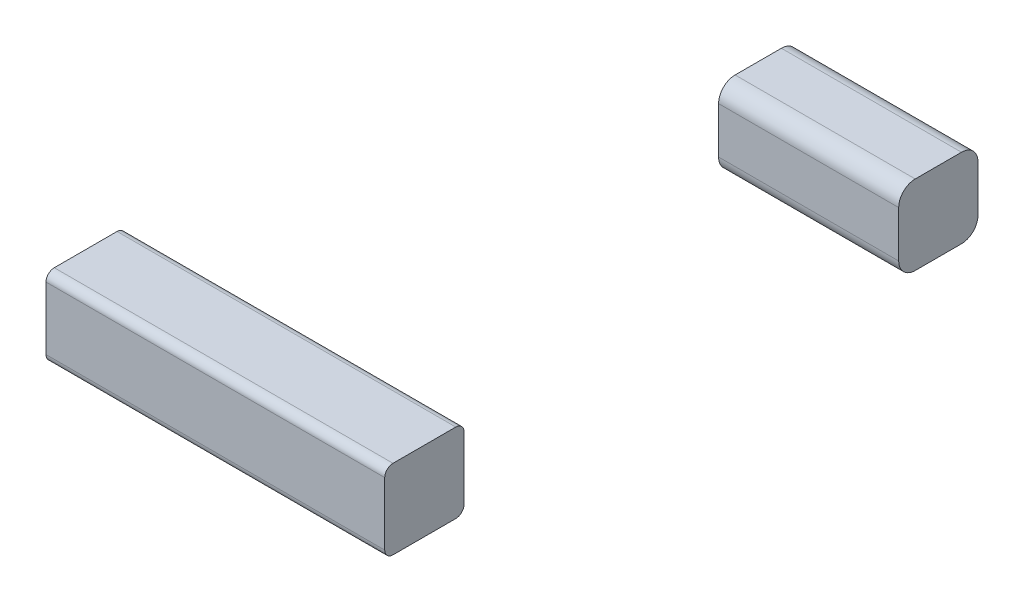
SolidWorks part; units mm, degrees
ref_plane "前视基准面" through (0, 0, 0) normal (0, 0, 1) x (1, 0, 0)
ref_plane "上视基准面" through (0, 0, 0) normal (0, 1, 0) x (1, 0, 0)
ref_plane "右视基准面" through (0, 0, 0) normal (1, 0, 0) x (0, 0, -1)
sketch "草图1" plane through (0, 0, 0) normal (0, 1, 0) x (1, 0, 0)
  line L1 (-12.2772, 15.4322) -> (-7.2772, 15.4322)
  line L2 (-12.2772, 15.4322) -> (-12.2772, 20.4322)
  line L3 (-12.2772, 20.4322) -> (-7.2772, 20.4322)
  line L4 (-7.2772, 15.4322) -> (-7.2772, 20.4322)
  line L5 (-12.2772, 15.4322) -> (-7.2772, 20.4322) construction
  line L6 (-12.2772, 20.4322) -> (-7.2772, 15.4322) construction
  circle A0 centre (-9.7772, 17.9322) radius 4.9
  dimension "D1" = 9.8
  dimension "D2" = 5
  dimension "D3" = 5
extrude "凸台-拉伸1" add sketch "草图1" along normal blind 5
sketch "草图2" plane through (0, 0, 0) normal (0, 1, 0) x (1, 0, 0)
  line L0 (-20.4935, 24.5269) -> (-10.4935, 24.5269)
  line L1 (-10.4935, 24.5269) -> (-10.4935, 29.5269)
  line L2 (-10.4935, 29.5269) -> (-20.4935, 29.5269)
  line L3 (-20.4935, 29.5269) -> (-20.4935, 24.5269)
  dimension "D1" = 10
  dimension "D2" = 5
extrude "凸台-拉伸2" add sketch "草图2" along normal blind 5 separate body
sketch "草图3" plane through (0, 5, 0) normal (0, 1, 0) x (1, 0, 0)
  circle A0 centre (-9.7772, 17.9322) radius 5.9149
extrude "切除-拉伸1" cut sketch "草图3" against normal blind 10
sketch "草图4" plane through (-20.4935, 0, 0) normal (-1, 0, 0) x (0, 0, 1)
  line L0 (-24.5269, 5) -> (-24.5269, 0) construction
  line L1 (-29.5269, 4.9) -> (-29.5269, 5)
  line L2 (-24.6269, 0) -> (-24.5269, 0)
  line L3 (-29.5269, 4.9) -> (-24.6269, 4.9)
  line L4 (-24.6269, 0) -> (-24.6269, 4.9)
  line L8 (-29.5269, 5) -> (-24.5269, 5)
  line L9 (-24.5269, 0) -> (-24.5269, 5)
  dimension "D1" = 4.9
  dimension "D2" = 0.1
extrude "切除-拉伸2" cut sketch "草图4" against normal blind 10
sketch "草图5" plane through (0, 0, 0) normal (1, 0, 0) x (0, 0, -1)
  line L2 (32.7248, 0) -> (37.5248, 0)
  line L3 (32.7248, 0) -> (32.7248, 4.8)
  line L4 (32.7248, 4.8) -> (37.5248, 4.8)
  line L5 (37.5248, 0) -> (37.5248, 4.8)
  line L6 (41.6044, 0) -> (46.2044, 0)
  line L7 (41.6044, 0) -> (41.6044, 4.6)
  line L8 (41.6044, 4.6) -> (46.2044, 4.6)
  line L9 (46.2044, 0) -> (46.2044, 4.6)
  line L10 (48.6704, 0) -> (53.1704, 0)
  line L11 (48.6704, 0) -> (48.6704, 4.5)
  line L12 (48.6704, 4.5) -> (53.1704, 4.5)
  line L13 (53.1704, 0) -> (53.1704, 4.5)
  dimension "D1" = 4.8
  dimension "D2" = 4.6
  dimension "D4" = 4.5
  dimension "D5" = 4.5
extrude "凸台-拉伸3" add sketch "草图5" along normal blind 10 separate body
fillet "圆角1" radius 0.5 4 edges at (-15.4935, 0, -29.5269) (-15.4935, 0, -24.6269) (-15.4935, 4.9, -29.5269) (-15.4935, 4.9, -24.6269)
fillet "圆角2" radius 0.5 4 edges at (5, 4.8, -37.5248) (5, 0, -37.5248) (5, 0, -32.7248) (5, 4.8, -32.7248)
fillet "圆角3" radius 0.5 4 edges at (5, 0, -41.6044) (5, 0, -46.2044) (5, 4.6, -41.6044) (5, 4.6, -46.2044)
fillet "圆角4" radius 0.5 4 edges at (5, 0, -48.6704) (5, 0, -53.1704) (5, 4.5, -48.6704) (5, 4.5, -53.1704)
sketch "草图6" plane through (-10.4935, 0, 0) normal (1, 0, 0) x (0, 0, -1)
  line L1 (24.6269, 4.9) -> (29.5269, 4.9)
  line L2 (24.6269, 4.9) -> (24.6269, 0)
  line L3 (24.6269, 0) -> (29.5269, 0)
  line L4 (29.5269, 4.9) -> (29.5269, 0)
  line L5 (24.6269, 4.9) -> (29.5269, 0) construction
  line L6 (24.6269, 0) -> (29.5269, 4.9) construction
  point P0 (27.0769, 2.45)
extrude "凸台-拉伸4" add sketch "草图6" along normal blind 20.5
fillet "圆角5" radius 1 4 edges at (-0.2435, 0, -24.6269) (-0.2435, 4.9, -29.5269) (-0.2435, 0, -29.5269) (-0.2435, 4.9, -24.6269)
sketch "草图8" plane through (0, 0, 0) normal (-1, 0, 0) x (0, 0, 1)
  line L4 (-33.2248, 4.8) -> (-37.0248, 4.8)
  line L5 (-37.5248, 4.3) -> (-37.5248, 0.5)
  line L6 (-37.0248, 0) -> (-33.2248, 0)
  line L7 (-32.7248, 0.5) -> (-32.7248, 4.3)
  line L8 (-33.2248, 4.8) -> (-37.0248, 4.8)
  line L9 (-37.5248, 4.3) -> (-37.5248, 0.5)
  line L10 (-37.0248, 0) -> (-33.2248, 0)
  line L11 (-32.7248, 0.5) -> (-32.7248, 4.3)
  arc A4 (-37.0248, 4.8) -> (-37.5248, 4.3) centre (-37.0248, 4.3) ccw
  arc A5 (-37.5248, 0.5) -> (-37.0248, 0) centre (-37.0248, 0.5) ccw
  arc A6 (-33.2248, 0) -> (-32.7248, 0.5) centre (-33.2248, 0.5) ccw
  arc A7 (-32.7248, 4.3) -> (-33.2248, 4.8) centre (-33.2248, 4.3) ccw
  arc A8 (-37.0248, 4.8) -> (-37.5248, 4.3) centre (-37.0248, 4.3) ccw
  arc A9 (-37.5248, 0.5) -> (-37.0248, 0) centre (-37.0248, 0.5) ccw
  arc A10 (-33.2248, 0) -> (-32.7248, 0.5) centre (-33.2248, 0.5) ccw
  arc A11 (-32.7248, 4.3) -> (-33.2248, 4.8) centre (-33.2248, 4.3) ccw
  dimension "D1" = 0
extrude "凸台-拉伸5" add sketch "草图8" along normal blind 10.5
sketch "草图9" plane through (0, 0, 0) normal (-1, 0, 0) x (0, 0, 1)
  circle A0 centre (-50.9868, 2.3556) radius 3.4026
extrude "切除-拉伸3" cut sketch "草图9" against normal blind 10.5
sketch "草图10" plane through (0, 0, 0) normal (-1, 0, 0) x (0, 0, 1)
  circle A0 centre (-43.7119, 2.4231) radius 4.3574
extrude "切除-拉伸4" cut sketch "草图10" against normal blind 10.5
sketch "草图11" plane through (-20.4935, 0, 0) normal (-1, 0, 0) x (0, 0, 1)
  circle A0 centre (-27.1499, 2.4287) radius 4.197
extrude "切除-拉伸5" cut sketch "草图11" against normal blind 100.5
sketch "草图12" plane through (0, 0, 0) normal (1, 0, 0) x (0, 0, -1)
  line L3 (62.9302, 0) -> (67.7302, 0)
  line L4 (62.9302, 0) -> (62.9302, 4.8)
  line L5 (62.9302, 4.8) -> (67.7302, 4.8)
  line L6 (67.7302, 0) -> (67.7302, 4.8)
  dimension "D2" = 4.8
extrude "凸台-拉伸6" add sketch "草图12" along normal blind 10.9 separate body
fillet "圆角6" radius 1 4 edges at (5.45, 0, -62.9302) (5.45, 4.8, -62.9302) (5.45, 0, -67.7302) (5.45, 4.8, -67.7302)
